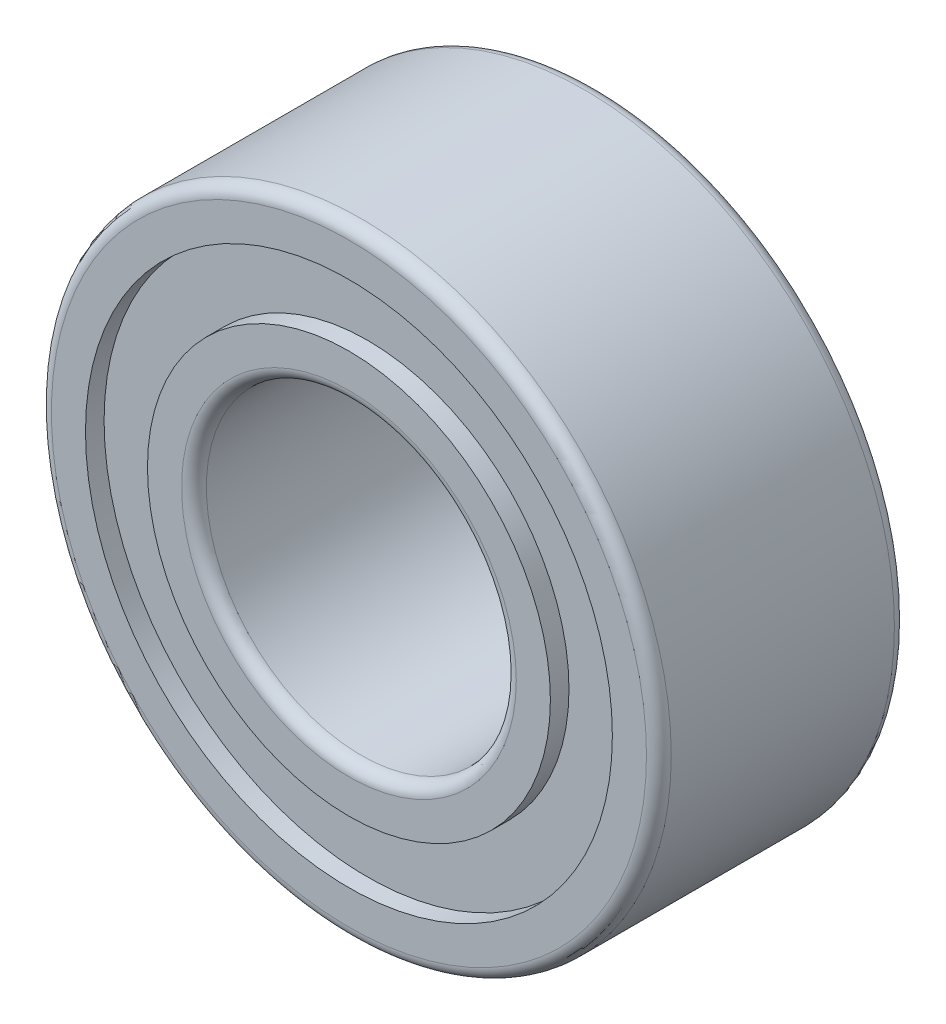
SolidWorks part; units mm, degrees
material "1.0401 (C15)"
ref_plane "Спереди" through (0, 0, 0) normal (0, 0, 1) x (1, 0, 0)
ref_plane "Сверху" through (0, 0, 0) normal (0, 1, 0) x (1, 0, 0)
ref_plane "Справа" through (0, 0, 0) normal (1, 0, 0) x (0, 0, -1)
sketch "Эскиз1" plane through (0, 0, 0) normal (0, 0, 1) x (1, 0, 0)
  circle A0 centre (0, 0) radius 5
  circle A3 centre (0, 0) radius 2.5
  dimension "D1" = 10
  dimension "D4" = 5
extrude "Бобышка-Вытянуть1" add sketch "Эскиз1" along normal blind 4
sketch "Эскиз4" plane through (0, 0, 4) normal (0, 0, 1) x (1, 0, 0)
  circle A6 centre (0, 0) radius 3.25
  circle A7 centre (0, 0) radius 4.25
  dimension "D1" = 8.5
  dimension "D2" = 6.5
extrude "Вырез-Вытянуть3" cut sketch "Эскиз4" against normal blind 0.3
sketch "Эскиз5" plane through (0, 0, 0) normal (0, 0, -1) x (-1, 0, 0)
  circle A0 centre (0, 0) radius 4.25 construction
  circle A1 centre (0, 0) radius 3.25 construction
  circle A2 centre (0, 0) radius 4.25
  circle A3 centre (0, 0) radius 3.25
extrude "Вырез-Вытянуть4" cut sketch "Эскиз5" against normal blind 0.3
fillet "Скругление2" radius 0.2 4 edges at (2.5, 0, 4) (2.5, 0, 0) (5, 0, 4) (5, 0, 0)
